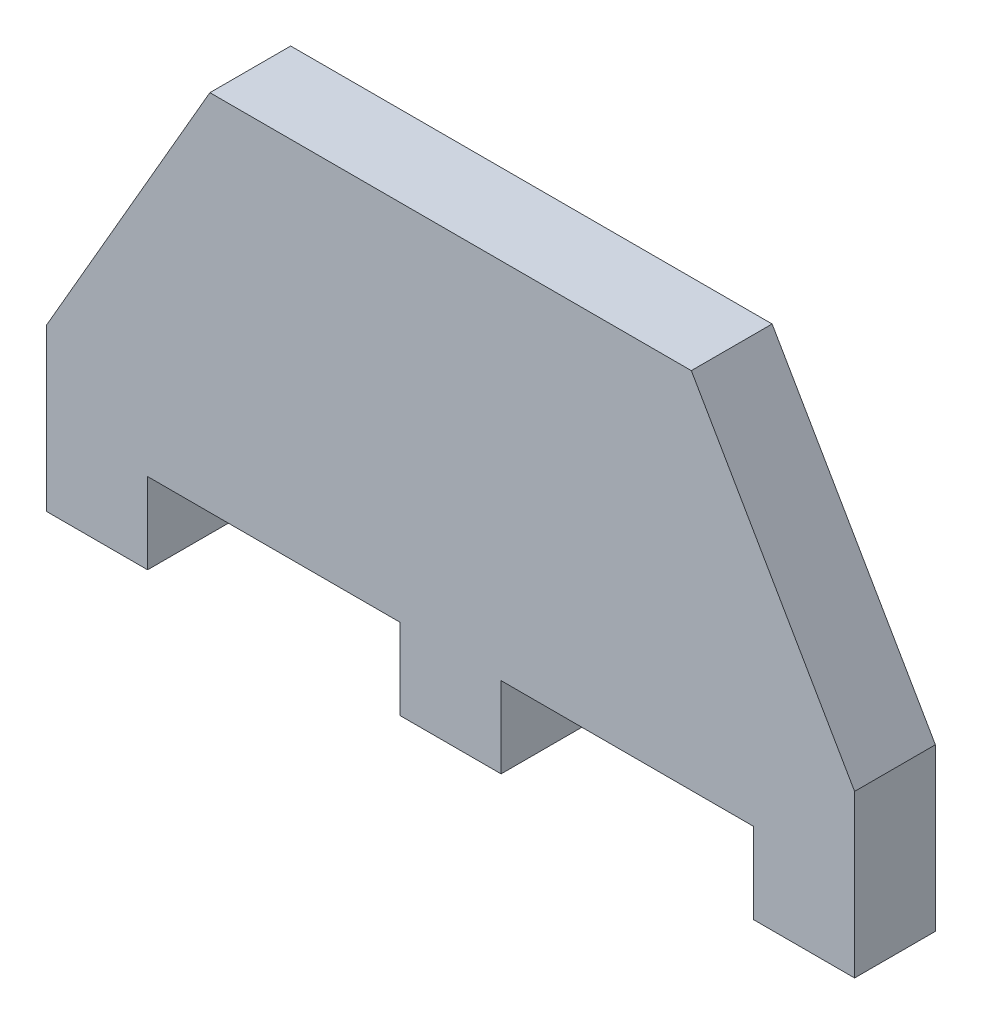
SolidWorks part; units mm, degrees
ref_plane "Front Plane" through (0, 0, 0) normal (0, 0, 1) x (1, 0, 0)
ref_plane "Top Plane" through (0, 0, 0) normal (0, 1, 0) x (1, 0, 0)
ref_plane "Right Plane" through (0, 0, 0) normal (1, 0, 0) x (0, 0, -1)
sketch "Sketch1" plane through (0, 0, 0) normal (0, 0, 1) x (1, 0, 0)
  line L0 (0, 0) -> (0, -10)
  line L1 (0, -10) -> (12.5, -10)
  line L2 (12.5, -10) -> (12.5, 0)
  line L3 (12.5, 0) -> (43.75, 0)
  line L4 (43.75, 0) -> (43.75, -10)
  line L5 (43.75, -10) -> (56.25, -10)
  line L6 (56.25, -10) -> (56.25, 0)
  line L7 (56.25, 0) -> (87.5, 0)
  line L8 (87.5, 0) -> (87.5, -10)
  line L9 (87.5, -10) -> (100, -10)
  line L10 (100, -10) -> (100, 0)
  line L11 (100, 0) -> (100, 10)
  line L12 (100, 10) -> (79.7927, 45)
  line L13 (79.7927, 45) -> (20.2073, 45)
  line L14 (20.2073, 45) -> (0, 10)
  line L15 (0, 10) -> (0, 0)
  line L16 (0, 0) -> (12.5, 0) construction
  line L17 (43.75, 0) -> (56.25, 0) construction
  line L18 (87.5, 0) -> (100, 0) construction
  dimension "D1" = 60
  dimension "D2" = 12.5
  dimension "D3" = 10
  dimension "D4" = 10
  dimension "D5" = 100
  dimension "D6" = 35
extrude "Boss-Extrude1" add sketch "Sketch1" along normal blind 10
